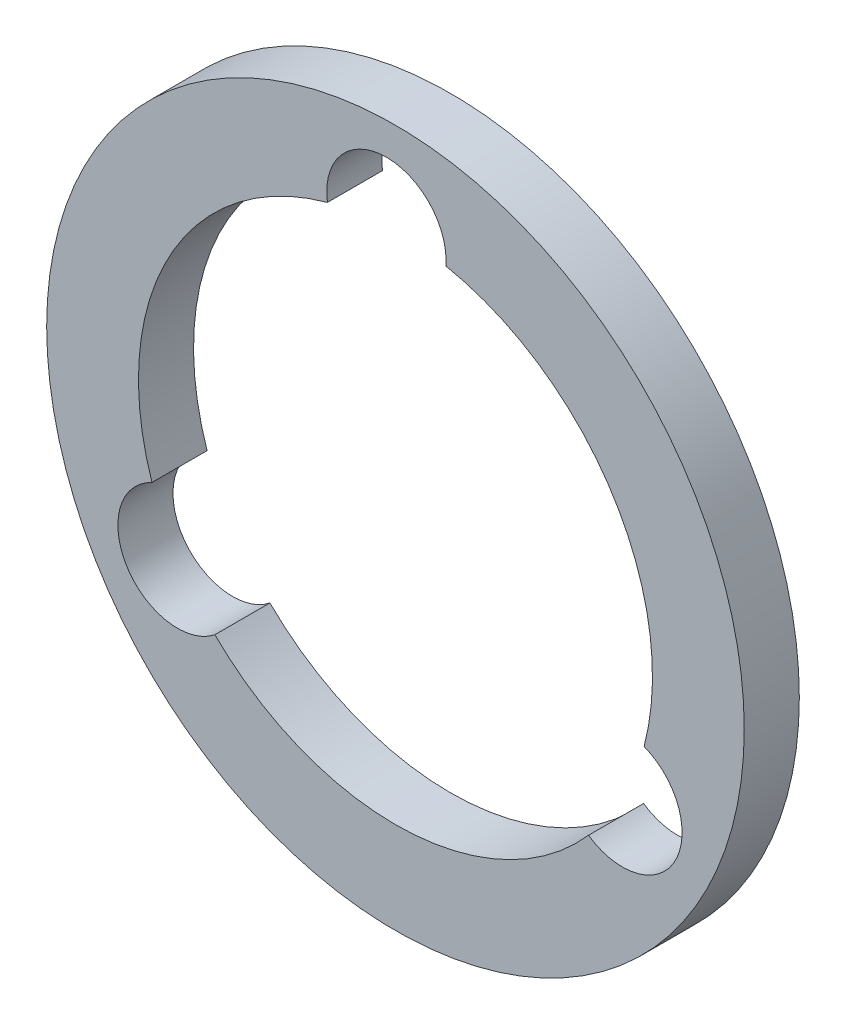
SolidWorks part; units mm, degrees
ref_plane "Plan de face" through (0, 0, 0) normal (0, 0, 1) x (1, 0, 0)
ref_plane "Plan de dessus" through (0, 0, 0) normal (0, 1, 0) x (1, 0, 0)
ref_plane "Plan de droite" through (0, 0, 0) normal (1, 0, 0) x (0, 0, -1)
sketch "Esquisse1" plane through (0, 0, 0) normal (0, 0, 1) x (1, 0, 0)
  circle A0 centre (0, 0) radius 19
  arc A29 (2.7455, 13.7281) -> (-3.7065, 13.5004) centre (-0.4938, 13.9913) ccw
  arc A31 (-3.7065, 13.5004) -> (-13.2617, -4.4864) centre (0, 0) ccw
  arc A32 (10.5162, -9.2418) -> (13.545, -3.5403) centre (12.3637, -6.568) ccw
  arc A33 (-13.2617, -4.4864) -> (-9.8385, -9.9602) centre (-11.8699, -7.4233) ccw
  arc A34 (-9.8385, -9.9602) -> (10.5162, -9.2418) centre (0, 0) ccw
  arc A35 (13.545, -3.5403) -> (2.7455, 13.7281) centre (0, 0) ccw
  point P15 (0, 0)
  point P31 (0, 0)
  dimension "D1" = 38
  dimension "D2" = 3
  dimension "D3" = 28
  dimension "D4" = 6.5
extrude "Boss.-Extru.2" add sketch "Esquisse1" along normal blind 3
